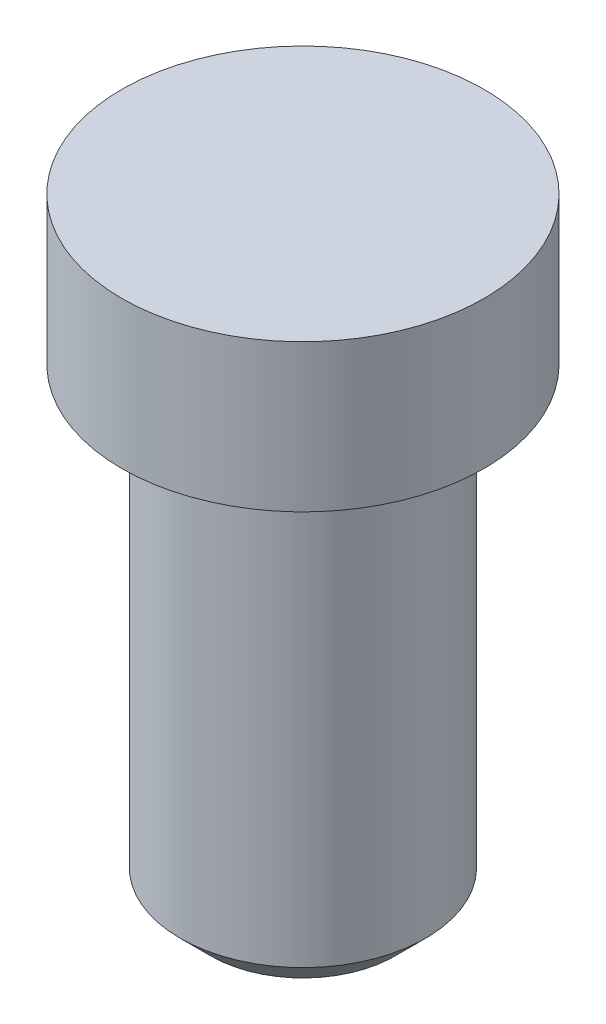
SolidWorks part; units mm, degrees
material "acero"
ref_plane "Alzado" through (0, 0, 0) normal (0, 0, 1) x (1, 0, 0)
ref_plane "Planta" through (0, 0, 0) normal (0, 1, 0) x (1, 0, 0)
ref_plane "Vista lateral" through (0, 0, 0) normal (1, 0, 0) x (0, 0, -1)
sketch "Croquis1" plane through (0, 0, 0) normal (0, 0, 1) x (1, 0, 0)
  line L0 (0, 0) -> (0, -60.9498) construction
  line L1 (0, 0) -> (2.95, 0)
  line L2 (2.95, 0) -> (2.95, -2.4)
  line L3 (2.95, -2.4) -> (2, -2.4)
  line L4 (2, -2.4) -> (2, -10)
  line L5 (2, -10) -> (0, -10)
  line L6 (0, -10) -> (0, 0)
  dimension "D1" = 10
  dimension "D2" = 2.4
  dimension "D3" = 5.9
  dimension "D4" = 4
revolve "Revolución1" add sketch "Croquis1" angle 360 about L0
chamfer "Chaflán1" distance 0.5 angle 45 1 edges at (0, -10, 2)
